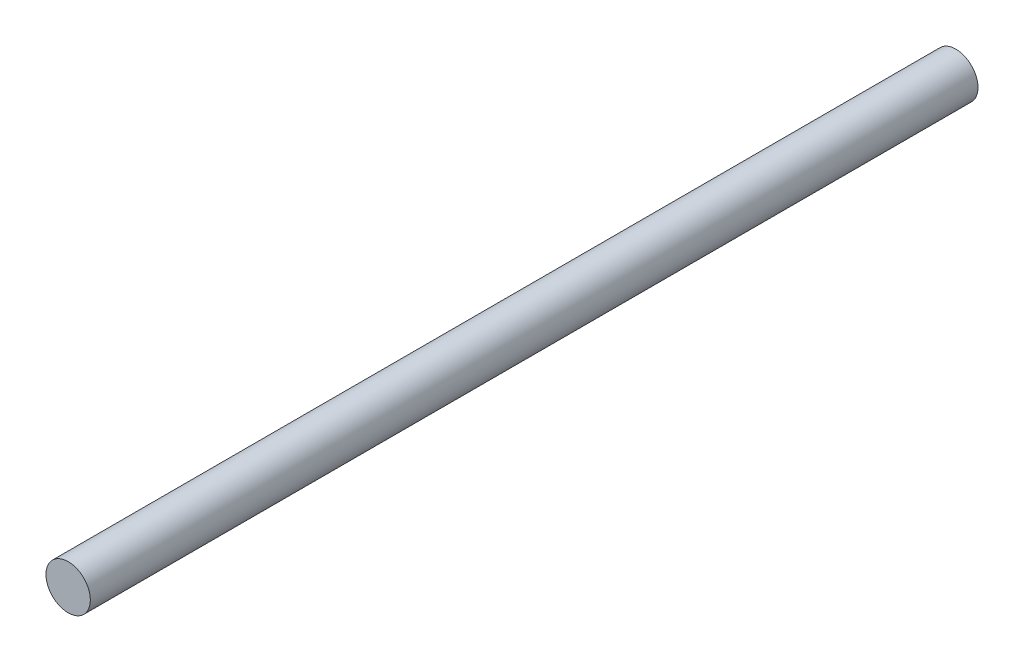
SolidWorks part; units mm, degrees
ref_plane "Front Plane" through (0, 0, 0) normal (0, 0, 1) x (1, 0, 0)
ref_plane "Top Plane" through (0, 0, 0) normal (0, 1, 0) x (1, 0, 0)
ref_plane "Right Plane" through (0, 0, 0) normal (1, 0, 0) x (0, 0, -1)
sketch "Sketch1" plane through (0, 0, 0) normal (0, 0, 1) x (1, 0, 0)
  circle A0 centre (0, 0) radius 1.5
extrude "Boss-Extrude1" add sketch "Sketch1" along normal blind 60
